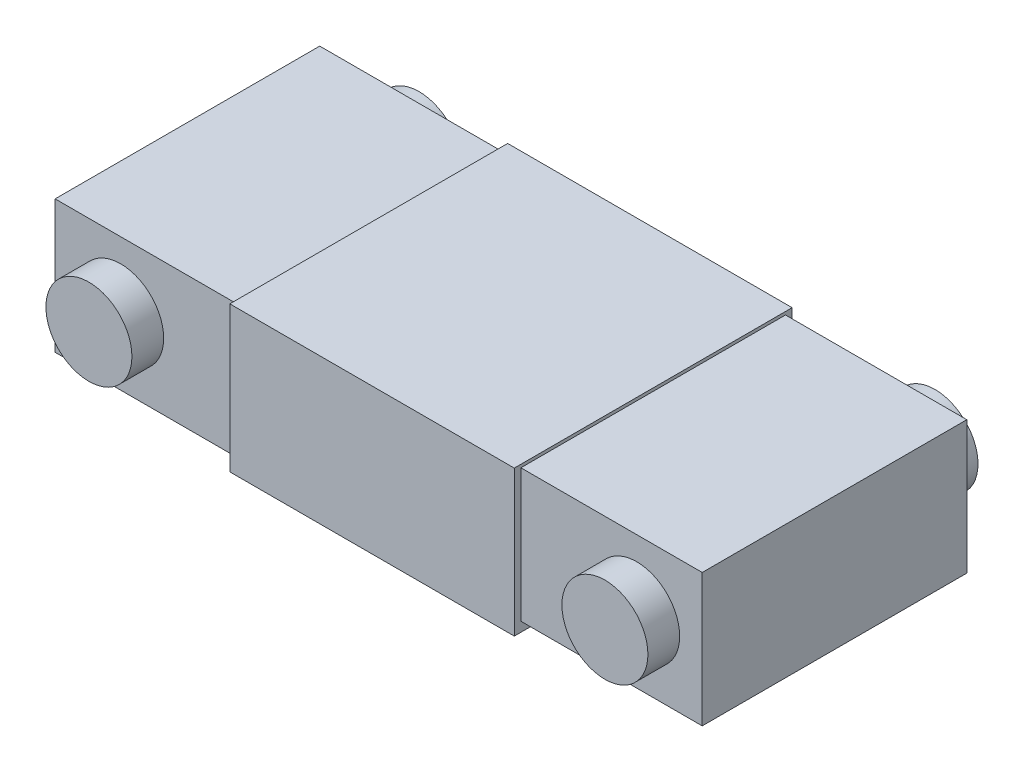
SolidWorks part; units mm, degrees
material "Окись алюминия"
ref_plane "Спереди" through (0, 0, 0) normal (0, 0, 1) x (1, 0, 0)
ref_plane "Сверху" through (0, 0, 0) normal (0, 1, 0) x (1, 0, 0)
ref_plane "Справа" through (0, 0, 0) normal (1, 0, 0) x (0, 0, -1)
other "Configuration Table"
sketch "Эскиз1" plane through (0, 0, 0) normal (0, 0, 1) x (1, 0, 0)
  line L0 (0, 0) -> (-9.91, 0) construction
  line L1 (17.5, -10.045) -> (17.5, -11.495)
  line L2 (-9.91, 10.045) -> (17.5, 10.045)
  line L3 (-9.91, 10.045) -> (-9.91, -10.045)
  line L4 (-9.91, -10.045) -> (17.5, -10.045)
  line L6 (60.5, 10.505) -> (17.5, 10.505)
  line L7 (60.5, 10.505) -> (60.5, 10.045)
  line L8 (60.5, -11.495) -> (17.5, -11.495)
  line L9 (17.5, 10.505) -> (17.5, 10.045)
  line L10 (39, -11.495) -> (39, 10.505) construction
  line L11 (87.91, -10.045) -> (60.5, -10.045)
  line L12 (87.91, 10.045) -> (87.91, -10.045)
  line L13 (87.91, 10.045) -> (60.5, 10.045)
  line L14 (60.5, -10.045) -> (60.5, -11.495)
  dimension "D1" = 9.91
  dimension "D2" = 20.09
  dimension "D3" = 27.41
  dimension "D4" = 0.46
  dimension "D5" = 22
  dimension "D6" = 43
extrude "Бобышка-Вытянуть1" add sketch "Эскиз1" along normal mid plane 40
sketch "Эскиз2" plane through (0, 0, 0) normal (0, 0, 1) x (1, 0, 0)
  line L0 (17.5, -11.495) -> (60.5, -11.495) construction
  line L1 (60.5, 10.505) -> (17.5, 10.505) construction
  line L2 (17.5, -11.495) -> (60.5, -11.495)
  line L3 (60.5, 10.505) -> (17.5, 10.505)
  line L4 (17.5, 10.505) -> (17.5, -11.495)
  line L5 (60.5, -11.495) -> (60.5, 10.505)
extrude "Бобышка-Вытянуть2" add sketch "Эскиз2" along normal mid plane 42 contours L3 L4 L2 L5
sketch "Эскиз3" plane through (0, 0, 0) normal (0, 0, 1) x (1, 0, 0)
  line L0 (39, 10.505) -> (39, -11.495) construction
  line L1 (60.5, 10.505) -> (17.5, 10.505) construction
  line L2 (17.5, -11.495) -> (60.5, -11.495) construction
  circle A0 centre (0, 0) radius 6.5
  circle A1 centre (78, 0) radius 6.5
  dimension "D1" = 13
extrude "Бобышка-Вытянуть4" add sketch "Эскиз3" along normal blind 24.8 and the other way blind 25.1
